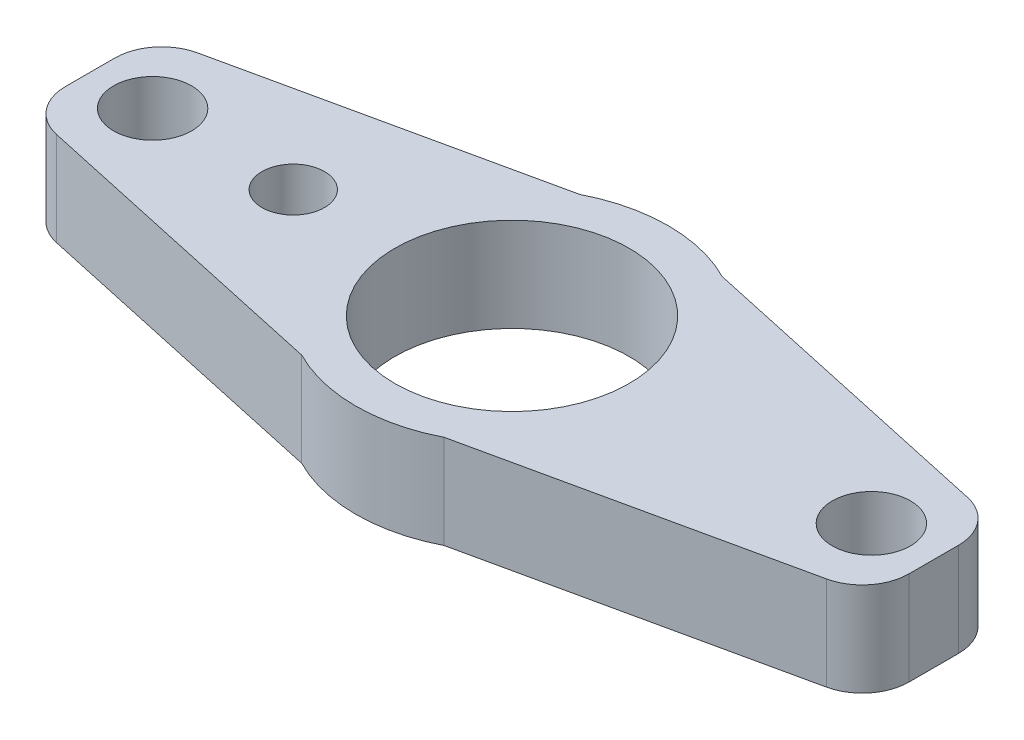
SolidWorks part; units mm, degrees
ref_plane "Front Plane" through (0, 0, 0) normal (0, 0, 1) x (1, 0, 0)
ref_plane "Top Plane" through (0, 0, 0) normal (0, 1, 0) x (1, 0, 0)
ref_plane "Right Plane" through (0, 0, 0) normal (1, 0, 0) x (0, 0, -1)
sketch "Sketch1" plane through (0, 0, 0) normal (0, 1, 0) x (1, 0, 0)
  line L0 (-2.2778, 4.451) -> (-13.5, 2)
  line L1 (-13.5, -5) -> (13.5, -5) construction
  line L2 (-13.5, -5) -> (-13.5, 5) construction
  line L3 (-13.5, 5) -> (13.5, 5) construction
  line L4 (13.5, -5) -> (13.5, 5) construction
  line L5 (-13.5, -5) -> (13.5, 5) construction
  line L6 (-13.5, 5) -> (13.5, -5) construction
  line L7 (2.2778, 4.451) -> (13.5, 2)
  line L8 (-13.5, 0) -> (13.5, 0) construction
  line L9 (2.2778, -4.451) -> (13.5, -2)
  line L10 (-2.2778, -4.451) -> (-13.5, -2)
  line L11 (-13.5, 2) -> (-13.5, -2)
  line L12 (13.5, 2) -> (13.5, -2)
  line L13 (0, 5) -> (0, -5) construction
  arc A0 (2.2778, 4.451) -> (-2.2778, 4.451) centre (0, 0) ccw
  circle A1 centre (0, 0) radius 3.75
  arc A2 (-2.2778, -4.451) -> (2.2778, -4.451) centre (0, 0) ccw
  circle A3 centre (-11.5, 0) radius 1.25
  circle A4 centre (11.5, 0) radius 1.25
  circle A5 centre (-7, 0) radius 1
  point P0 (0, 0)
  dimension "D3" = 7.5
  dimension "D6" = 2.5
  dimension "D7" = 2
  dimension "D9" = 2
  dimension "D1" = 27
  dimension "D2" = 10
  dimension "D4" = 4
  dimension "D5" = 4
  dimension "D8" = 7
  dimension "D10" = 11.2222
  dimension "D11" = 11.2222
extrude "Boss-Extrude1" add sketch "Sketch1" along normal blind 3
fillet "Fillet1" radius 1.5 4 edges at (13.5, 1.5, 2) (13.5, 1.5, -2) (-13.5, 1.5, 2) (-13.5, 1.5, -2)
